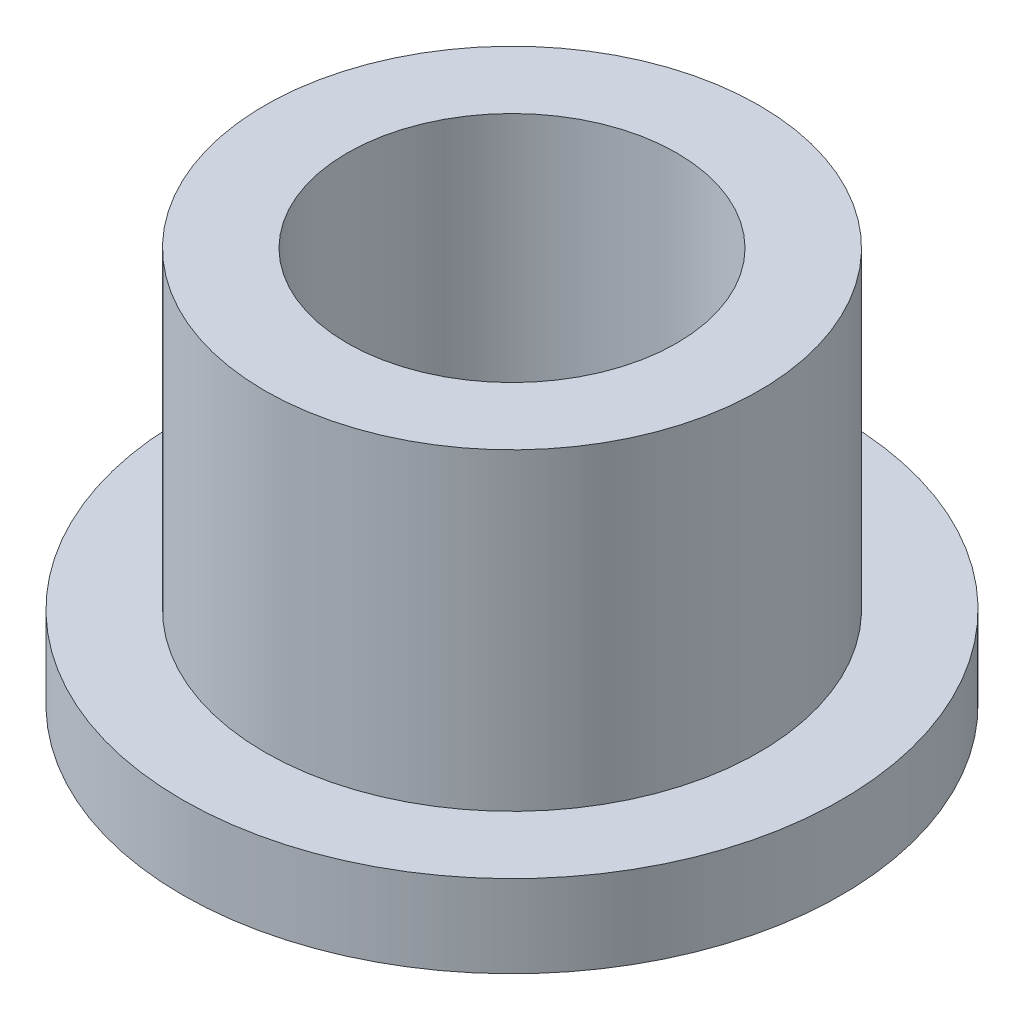
SolidWorks part; units mm, degrees
ref_plane "Front" through (0, 0, 0) normal (0, 0, 1) x (1, 0, 0)
ref_plane "Top" through (0, 0, 0) normal (0, 1, 0) x (1, 0, 0)
ref_plane "Right" through (0, 0, 0) normal (1, 0, 0) x (0, 0, -1)
sketch "Sketch1" plane through (0, 0, 0) normal (0, 1, 0) x (1, 0, 0)
  circle A0 centre (0, 0) radius 3.175
  circle A1 centre (0, 0) radius 4.7625
  circle A2 centre (0, 0) radius 6.35
  dimension "ID" = 6.35
  dimension "OD" = 9.525
  dimension "FlangeOD" = 12.7
sketch "Sketch2" plane through (0, 0, 0) normal (0, 1, 0) x (1, 0, 0)
  circle A0 centre (0, 0) radius 3.175 construction
  circle A1 centre (0, 0) radius 4.7625 construction
  circle A2 centre (0, 0) radius 3.175
  circle A3 centre (0, 0) radius 4.7625
extrude "Boss-Extrude1" add sketch "Sketch2" along normal blind 7.62
sketch "Sketch3" plane through (0, 0, 0) normal (0, 1, 0) x (1, 0, 0)
  circle A0 centre (0, 0) radius 6.35 construction
  circle A1 centre (0, 0) radius 4.7625 construction
  circle A2 centre (0, 0) radius 6.35
  circle A3 centre (0, 0) radius 4.7625
extrude "Boss-Extrude2" add sketch "Sketch3" along normal blind 1.5875
